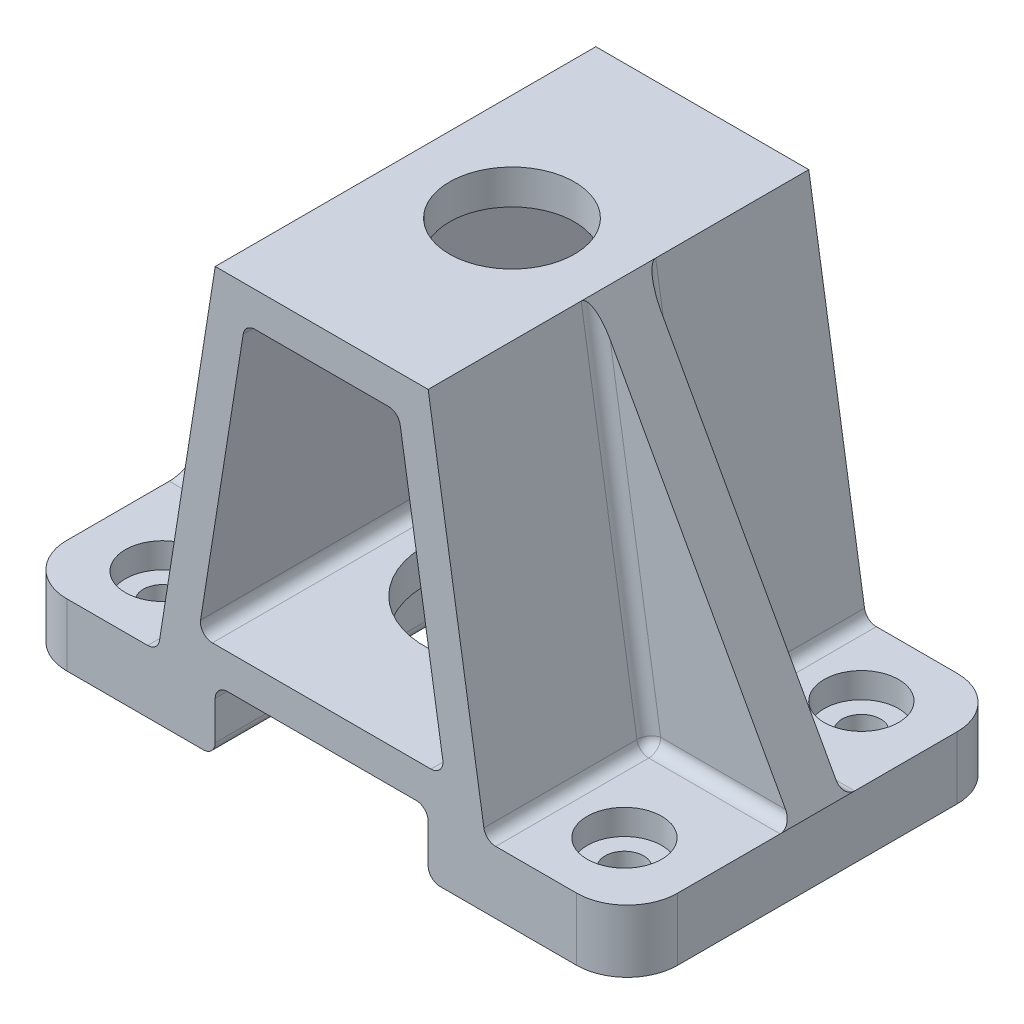
SolidWorks part; units mm, degrees
ref_plane "Frontal" through (0, 0, 0) normal (0, 0, 1) x (1, 0, 0)
ref_plane "Horizontal" through (0, 0, 0) normal (0, 1, 0) x (1, 0, 0)
ref_plane "Profile" through (0, 0, 0) normal (1, 0, 0) x (0, 0, -1)
sketch "Sketch1" plane through (0, 0, 0) normal (0, 1, 0) x (1, 0, 0)
  line L1 (-75.9034, 43.6425) -> (40.6826, 43.6425)
  line L2 (-75.9034, 43.6425) -> (-75.9034, -29.0015)
  line L3 (-75.9034, -29.0015) -> (40.6826, -29.0015)
  line L4 (40.6826, 43.6425) -> (40.6826, -29.0015)
  dimension "D1" = 72.644
  dimension "D2" = 116.586
extrude "Extrude1" add sketch "Sketch1" along normal blind 11.938
sketch "Sketch2" plane through (0, 11.938, 0) normal (0, 1, 0) x (-1, 0, 0)
  line L1 (75.9034, 29.0015) -> (-40.6826, 29.0015) construction
  line L2 (-40.6826, 29.0015) -> (-40.6826, -43.6425) construction
  circle A0 centre (-26.4586, 15.2855) radius 9.5177
  dimension "D1" = 13.716
  dimension "D2" = 14.224
extrude "Cut-Extrude1" cut sketch "Sketch2" against normal through all
sketch "Sketch4" plane through (0, 11.938, 0) normal (0, 1, 0) x (-1, 0, 0)
  line L0 (17.6104, -43.6425) -> (17.6104, 29.0015) construction
  line L1 (-40.6826, -43.6425) -> (75.9034, -43.6425) construction
  line L2 (75.9034, 29.0015) -> (-40.6826, 29.0015) construction
  line L3 (75.9034, -7.3205) -> (-40.6826, -7.3205) construction
  line L4 (75.9034, -43.6425) -> (75.9034, 29.0015) construction
  line L5 (-40.6826, 29.0015) -> (-40.6826, -43.6425) construction
ref_plane "Plane1" through (0, 81.026, 0) normal (0, 1, 0) x (-1, 0, 0)
sketch "Sketch5" plane through (0, 81.026, 0) normal (0, 1, 0) x (-1, 0, 0)
  line L0 (-40.6826, -43.6425) -> (75.9034, -43.6425) construction
  line L1 (37.9304, -43.6425) -> (-2.7096, -43.6425)
  line L2 (37.9304, -43.6425) -> (37.9304, 29.0015)
  line L3 (37.9304, 29.0015) -> (-2.7096, 29.0015)
  line L4 (-2.7096, -43.6425) -> (-2.7096, 29.0015)
  line L5 (75.9034, 29.0015) -> (-40.6826, 29.0015) construction
  point P10 (17.6104, -43.6425)
  dimension "D1" = 40.64
extrude "Extrude3" add sketch "Sketch5" against normal blind 69.088 draft 9 draft outward yes
sketch "Sketch6" plane through (0, 0, 0) normal (0, -1, 0) x (1, 0, 0)
  line L0 (-75.9034, 29.0015) -> (40.6826, 29.0015) construction
  line L1 (-37.9304, 29.0015) -> (2.7096, 29.0015)
  line L2 (-37.9304, 29.0015) -> (-37.9304, -43.6425)
  line L3 (-37.9304, -43.6425) -> (2.7096, -43.6425)
  line L4 (2.7096, 29.0015) -> (2.7096, -43.6425)
  line L5 (40.6826, -43.6425) -> (-75.9034, -43.6425) construction
  point P8 (-17.6104, 29.0015)
extrude "Cut-Extrude3" cut sketch "Sketch6" against normal blind 11.938
sketch "Sketch7" plane through (0, 11.938, 0) normal (0, -1, 0) x (1, 0, 0)
  line L0 (2.7096, 29.0015) -> (40.6826, 29.0015) construction
  line L1 (-52.5296, 43.5495) -> (17.0934, 43.5495)
  line L2 (-52.5296, 43.5495) -> (-52.5296, 29.0015)
  line L3 (-52.5296, 29.0015) -> (17.0934, 29.0015)
  line L4 (17.0934, 43.5495) -> (17.0934, 29.0015)
extrude "Cut-Extrude4" cut sketch "Sketch7" against normal through all
sketch "Sketch8" plane through (0, 11.938, 0) normal (0, -1, 0) x (1, 0, 0)
  line L0 (-37.9304, -43.6425) -> (-75.9034, -43.6425) construction
  line L1 (-56.323, -43.6425) -> (27.8155, -43.6425)
  line L2 (-56.323, -43.6425) -> (-56.323, -59.6707)
  line L3 (-56.323, -59.6707) -> (27.8155, -59.6707)
  line L4 (27.8155, -43.6425) -> (27.8155, -59.6707)
extrude "Cut-Extrude5" cut sketch "Sketch8" against normal through all
shell "Shell1" thickness 6.604
sketch "Sketch9" plane through (0, 11.938, 0) normal (0, -1, 0) x (1, 0, 0)
  line L0 (-17.6104, -43.6425) -> (-17.6104, 29.0015) construction
  circle A0 centre (-17.6104, -7.3205) radius 16.637
extrude "Cut-Extrude6" cut sketch "Sketch9" against normal up to next
sketch "Sketch10" plane through (0, 81.026, 0) normal (0, 1, 0) x (-1, 0, 0)
  line L0 (17.6104, -43.6425) -> (17.6104, 29.0015) construction
  circle A0 centre (17.6104, -7.3205) radius 11.938
extrude "Cut-Extrude7" cut sketch "Sketch10" against normal up to next
sketch "Sketch14" plane through (0, 0, 0) normal (0, -1, 0) x (1, 0, 0)
  circle A0 centre (26.4586, 15.2855) radius 9.5177
extrude "Extrude5" add sketch "Sketch14" against normal blind 11.938
sketch "Sketch15" plane through (0, 0, 0) normal (0, -1, 0) x (1, 0, 0)
  line L0 (2.7096, 29.0015) -> (40.6826, 29.0015) construction
  line L1 (40.6826, 29.0015) -> (40.6826, -43.6425) construction
  circle A0 centre (26.4586, 15.2855) radius 3.683
  dimension "D1" = 13.716
  dimension "D2" = 14.224
extrude "Cut-Extrude10" cut sketch "Sketch15" against normal through all
sketch "Sketch16" plane through (0, 11.938, 0) normal (0, 1, 0) x (-1, 0, 0)
  circle A0 centre (-26.4586, 15.2855) radius 7.112
extrude "Cut-Extrude11" cut sketch "Sketch16" against normal blind 4.826
sketch "Sketch17" plane through (0, 11.938, 0) normal (0, 1, 0) x (-1, 0, 0)
  line L0 (-26.4586, 15.2855) -> (-26.4586, -39.1617) construction
  line L1 (-26.4586, 15.2855) -> (64.0369, 15.2855) construction
pattern_linear "LPattern2" count 2 spacing 45.212 along (0, 0, -1) count 2 spacing 88.138 along (-1, 0, 0) of "Cut-Extrude10", "Cut-Extrude11"
fillet "Fillet1" radius 9.652 4 edges at (-75.9034, 5.969, -43.6425) (40.6826, 5.969, -43.6425) (40.6826, 5.969, 29.0015) (-75.9034, 5.969, 29.0015)
fillet "Fillet2" radius 2.286 4 edges at (5.9198, 18.542, -7.3205) (-41.1405, 18.542, -7.3205) (-32.29, 74.422, -7.3205) (-2.9307, 74.422, -7.3205)
fillet "Fillet3" radius 2.286 2 edges at (-37.9304, 11.938, -7.3205) (2.7096, 11.938, -7.3205)
ref_plane "Plane2" through (0, 0, -7.3152) normal (0, 0, 1) x (1, 0, 0)
sketch "Sketch21" plane through (0, 0, -7.3152) normal (0, 0, 1) x (1, 0, 0)
  line L0 (2.7096, 81.026) -> (40.6826, 11.938)
  line L1 (39.9542, 81.026) -> (-39.9542, 81.026) construction
  line L2 (13.6521, 11.938) -> (2.7096, 81.026) construction
rib "Rib1" sketch "Sketch21" sketch "Sketch21" thickness 9.652 extrusion direction parallel to sketch draft on no parameters "D1"=9.652
sketch "Sketch22" plane through (0, 0, -7.3152) normal (0, 0, 1) x (1, 0, 0)
  line L0 (-37.9304, 81.026) -> (-75.9034, 11.938)
  line L1 (39.9542, 81.026) -> (-39.9542, 81.026) construction
  line L2 (-37.9304, 81.026) -> (-48.8728, 11.938) construction
rib "Rib2" sketch "Sketch22" sketch "Sketch22" thickness 9.652 extrusion direction parallel to sketch draft on no parameters "D1"=9.652
fillet "Fillet4" radius 2.286 12 edges at (13.6521, 11.938, 13.2561) (-48.8728, 11.938, -27.8919) (13.6521, 11.938, -27.8919) (8.1809, 46.482, -12.1412) (27.1674, 11.938, -12.1412) (8.1809, 46.482, -2.4892) (27.1674, 11.938, -2.4892) (-48.8728, 11.938, 13.2561) (-62.3881, 11.938, -2.4892) (-43.4016, 46.482, -2.4892) (-62.3881, 11.938, -12.1412) (-43.4016, 46.482, -12.1412)
fillet "Fillet5" radius 2.286 2 edges at (-37.9304, 0, -7.3205) (2.7096, 0, -7.3205)
